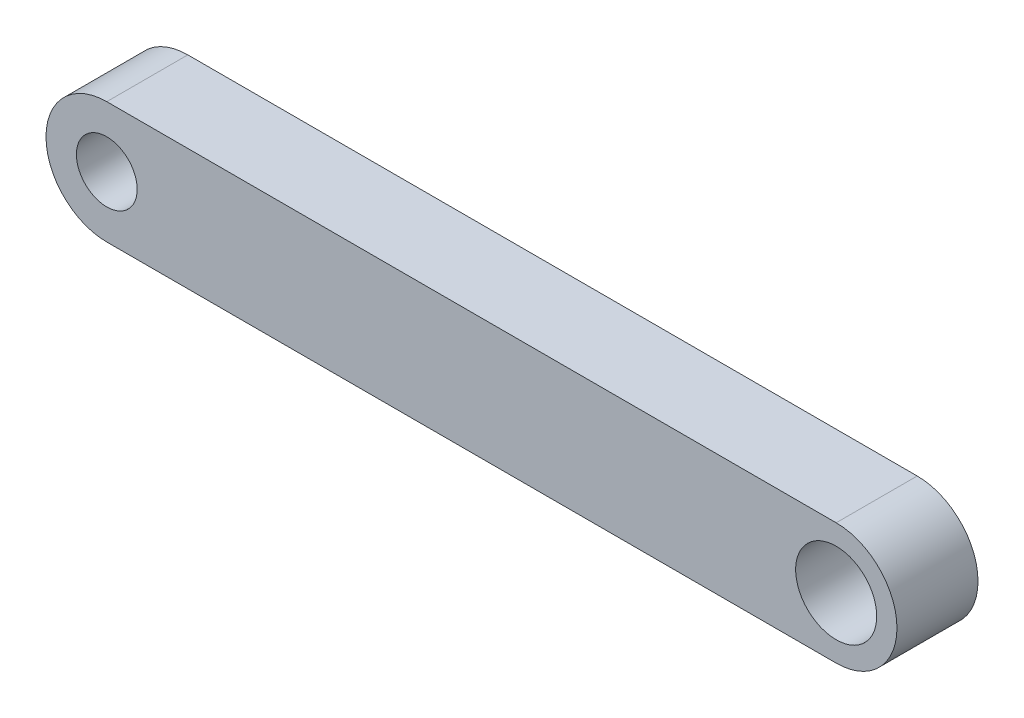
SolidWorks part; units mm, degrees
ref_plane "Front Plane" through (0, 0, 0) normal (0, 0, 1) x (1, 0, 0)
ref_plane "Top Plane" through (0, 0, 0) normal (0, 1, 0) x (1, 0, 0)
ref_plane "Right Plane" through (0, 0, 0) normal (1, 0, 0) x (0, 0, -1)
sketch "Sketch2" plane through (0, 0, 0) normal (0, 0, 1) x (1, 0, 0)
  line L0 (0, 3) -> (-36, 3)
  line L1 (0, -3) -> (-36, -3)
  line L2 (-18, 3) -> (-18, -3) construction
  line L3 (0, 3) -> (0, -3) construction
  line L4 (-36, 3) -> (-36, -3) construction
  circle A0 centre (0, 0) radius 2
  arc A1 (0, -3) -> (0, 3) centre (0, 0) ccw
  arc A2 (-36, -3) -> (-36, 3) centre (-36, 0) cw
  circle A4 centre (-36, 0) radius 1.5
  dimension "D1" = 4
  dimension "D2" = 6
  dimension "D4" = 3
  dimension "D3" = 36
extrude "Boss-Extrude1" add sketch "Sketch2" along normal blind 4
